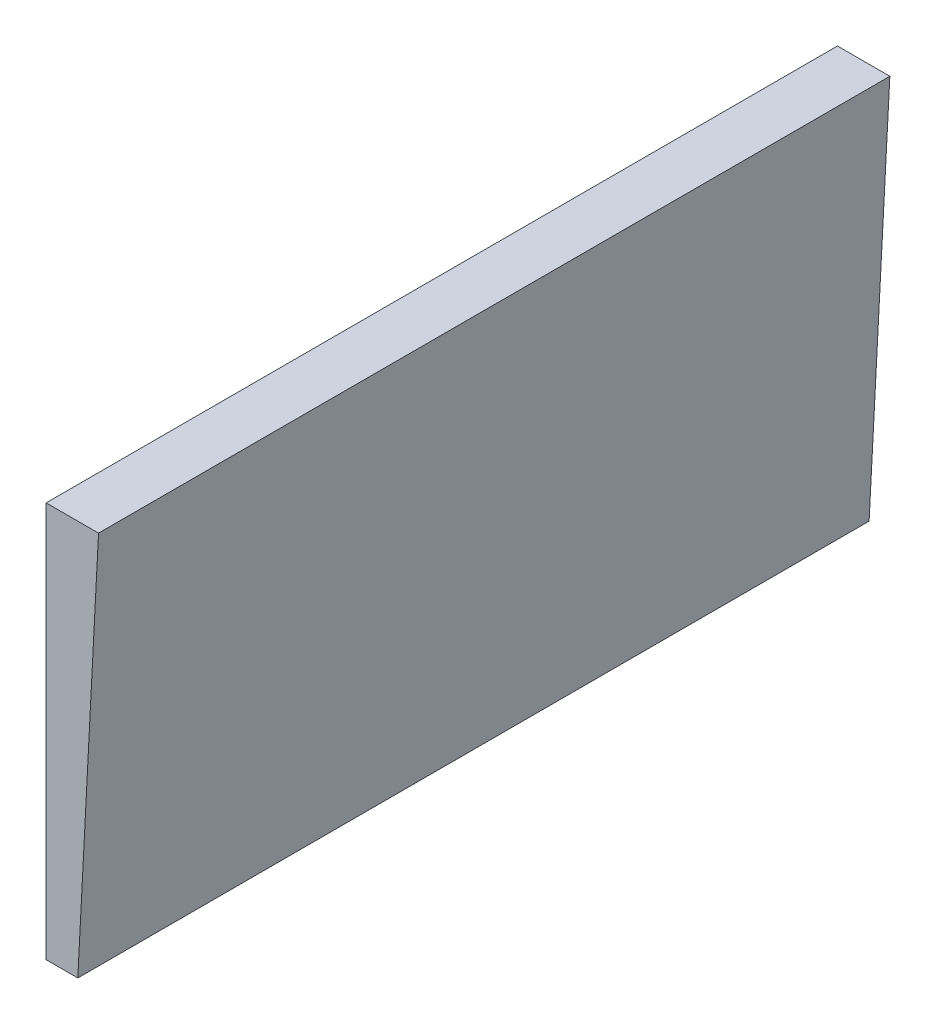
SolidWorks part; units mm, degrees
ref_plane "Front Plane" through (0, 0, 0) normal (0, 0, 1) x (1, 0, 0)
ref_plane "Top Plane" through (0, 0, 0) normal (0, 1, 0) x (1, 0, 0)
ref_plane "Right Plane" through (0, 0, 0) normal (1, 0, 0) x (0, 0, -1)
sketch "Sketch1" plane through (0, 0, 0) normal (0, 0, 1) x (1, 0, 0)
  line L0 (0, 25) -> (0, 0) construction
  line L1 (0, 0) -> (1.3102, 25)
  line L2 (1.3102, 25) -> (0, 25)
  line L3 (0, 25) -> (-2, 25)
  line L5 (-2, 25) -> (-2, 0)
  line L7 (-2, 0) -> (0, 0)
  dimension "D1" = 3
  dimension "D2" = 25
  dimension "D3" = 2
extrude "Boss-Extrude1" add sketch "Sketch1" along normal blind 50
